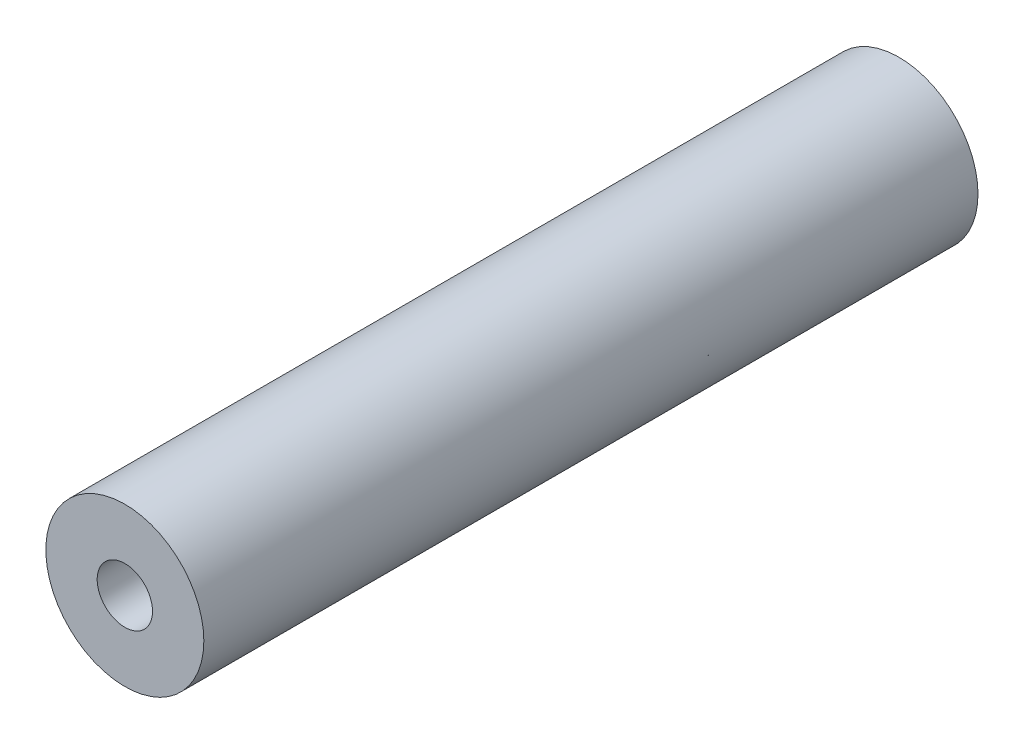
SolidWorks part; units mm, degrees
ref_plane "Front Plane" through (0, 0, 0) normal (0, 0, 1) x (1, 0, 0)
ref_plane "Top Plane" through (0, 0, 0) normal (0, 1, 0) x (1, 0, 0)
ref_plane "Right Plane" through (0, 0, 0) normal (1, 0, 0) x (0, 0, -1)
sketch "Sketch1" plane through (0, 0, 0) normal (0, 0, 1) x (1, 0, 0)
  circle A0 centre (0, 0) radius 10
  circle A1 centre (0, 0) radius 7.5
  dimension "D1" = 15
  dimension "D2" = 20
extrude "Boss-Extrude1" add sketch "Sketch1" along normal blind 98
sketch "Sketch2" plane through (0, 0, 98) normal (0, 0, 1) x (1, 0, 0)
  circle A0 centre (0, 0) radius 7.5
extrude "Boss-Extrude2" add sketch "Sketch2" against normal blind 5
sketch "Sketch3" plane through (0, 0, 98) normal (0, 0, 1) x (1, 0, 0)
  circle A0 centre (0, 0) radius 3.5
  dimension "D1" = 7
extrude "Cut-Extrude1" cut sketch "Sketch3" against normal blind 5
sketch "Sketch4" plane through (0, 0, 0) normal (0, 0, -1) x (-1, 0, 0)
  circle A0 centre (0, 0) radius 7.5
extrude "Boss-Extrude4" add sketch "Sketch4" against normal blind 3
sketch "Sketch5" plane through (0, 0, 0) normal (0, 0, -1) x (-1, 0, 0)
  circle A0 centre (0, 0) radius 6.6882
extrude "Cut-Extrude2" cut sketch "Sketch5" against normal blind 5
